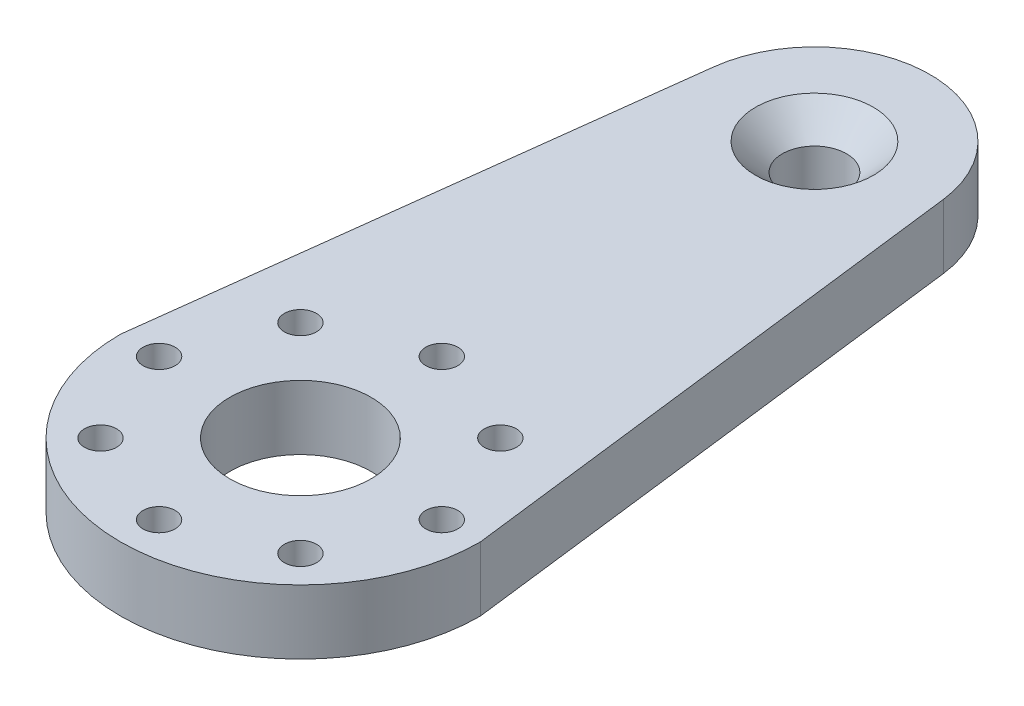
SolidWorks part; units mm, degrees
material "3003 Alloy"
ref_plane "Front Plane" through (0, 0, 0) normal (0, 0, 1) x (1, 0, 0)
ref_plane "Top Plane" through (0, 0, 0) normal (0, 1, 0) x (1, 0, 0)
ref_plane "Right Plane" through (0, 0, 0) normal (1, 0, 0) x (0, 0, -1)
sketch "Sketch1" plane through (0, 0, 0) normal (0, 1, 0) x (1, 0, 0)
  line L0 (0, 0) -> (0, 40) construction
  line L1 (-14, 0) -> (-14, 40)
  line L2 (14, 0) -> (14, 40)
  arc A0 (-14, 0) -> (14, 0) centre (0, 0) ccw
  arc A1 (14, 40) -> (-14, 40) centre (0, 40) ccw
  circle A2 centre (0, 40) radius 2.5
  circle A3 centre (0, 0) radius 5.5
  point P3 (0, 20)
  dimension "D3" = 11
  dimension "D4" = 5
  dimension "D1" = 40
  dimension "D2" = 28
extrude "Boss-Extrude1" add sketch "Sketch1" along normal blind 5
sketch "Sketch2" plane through (0, 5, 0) normal (0, 1, 0) x (1, 0, 0)
  line L0 (0, 0) -> (0, 11) construction
  circle A0 centre (0, 11) radius 1.25
  circle A1 centre (7.7782, 7.7782) radius 1.25
  circle A2 centre (11, 0) radius 1.25
  circle A3 centre (7.7782, -7.7782) radius 1.25
  circle A4 centre (0, -11) radius 1.25
  circle A5 centre (-7.7782, -7.7782) radius 1.25
  circle A6 centre (-11, 0) radius 1.25
  circle A7 centre (-7.7782, 7.7782) radius 1.25
  circle A8 centre (0, 0) radius 11 construction
  point P21 (0, 0)
  dimension "D1" = 2.5
  dimension "D2" = 11
  dimension "D3" = 8
extrude "Cut-Extrude1" cut sketch "Sketch2" against normal through all
sketch "Sketch3" plane through (0, 5, 0) normal (0, 1, 0) x (1, 0, 0)
  line L0 (-14, 0) -> (-8.9324, 41.1013)
  line L1 (14, 0) -> (8.9324, 41.1013)
  line L2 (-14, 40) -> (-14, 0) construction
  line L3 (14, 0) -> (14, 40) construction
  line L4 (-14, 40) -> (-14, 0)
  line L5 (14, 0) -> (14, 40)
  arc A1 (14, 40) -> (-14, 40) centre (0, 40) ccw construction
  circle A3 centre (0, 40) radius 9
  arc A4 (14, 40) -> (-14, 40) centre (0, 40) ccw
  line M12 (14, 0) -> (14, 40)
  arc M13 (14, 40) -> (-14, 40) centre (0, 40) ccw
  line M14 (-14, 40) -> (-14, 0)
  dimension "D1" = 18
extrude "Cut-Extrude2" cut sketch "Sketch3" against normal through all contours A3 L1 L0 M12 M13 M14
hole_wizard "CSK for M4 Hex Socket Countersunk Head Screw2" positions "Sketch6" profile "Sketch5" countersink size "M4" standard "DIN" end condition through all
sketch "Sketch6" plane through (0, 5, 0) normal (0, 1, 0) x (1, 0, 0)
  point P0 (0, 40)
sketch "Sketch5" plane through (0, 5, -40) normal (1, 0, 0) x (0, 0, 1)
  line L0 (0, 0) -> (0, 5)
  line L1 (0, 5) -> (2.25, 5)
  line L2 (2.25, 5) -> (2.25, 2.34)
  line L3 (2.25, 2.34) -> (4.59, 0)
  line L5 (4.59, 0) -> (0, 0)
  line L6 (-2.25, 2.34) -> (-4.59, 0) construction
  line L11 (0, -6.35) -> (0, 107.95) construction
  dimension "Thru Hole Dia." = 4.5
  dimension "Thru Hole Depth" = 5
  dimension "Near C'Sink Dia." = 9.18
  dimension "Near C'Sink Angle" = 90
